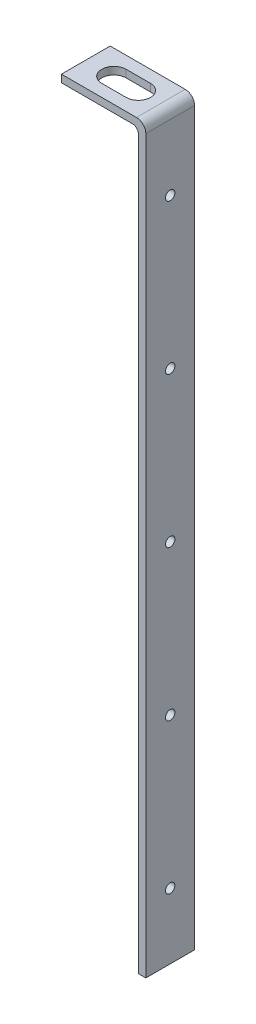
SolidWorks part; units mm, degrees
material "AISI 304"
ref_plane "Front Plane" through (0, 0, 0) normal (0, 0, 1) x (1, 0, 0)
ref_plane "Top Plane" through (0, 0, 0) normal (0, 1, 0) x (1, 0, 0)
ref_plane "Right Plane" through (0, 0, 0) normal (1, 0, 0) x (0, 0, -1)
sketch "Sketch1" plane through (0, 0, 0) normal (0, 0, 1) x (1, 0, 0)
  line L0 (0, 0) -> (0, 395)
  line L1 (0, 395) -> (-45, 395)
  line L6 (-4, 0) -> (-4, 391)
  line L7 (-4, 391) -> (-45, 391)
  line L8 (-45, 395) -> (-45, 391)
  line L9 (-4, 0) -> (0, 0)
  dimension "D1" = 395
  dimension "D2" = 45
  dimension "D3" = 4
extrude "Boss-Extrude1" add sketch "Sketch1" along normal blind 26
sketch "Sketch2" plane through (0, 0, 0) normal (1, 0, 0) x (0, 0, -1)
  line L1 (-26, 0) -> (0, 0) construction
  circle A0 centre (-13, 195) radius 2.5
  circle A1 centre (-13, 115) radius 2.5
  circle A2 centre (-13, 35) radius 2.5
  circle A3 centre (-13, 275) radius 2.5
  circle A4 centre (-13, 355) radius 2.5
  point P10 (-13, 0)
  dimension "D4" = 5
  dimension "D1" = 35
  dimension "D2" = 80
  dimension "D3" = 80
  dimension "D5" = 80
  dimension "D6" = 80
extrude "Cut-Extrude1" cut sketch "Sketch2" against normal through all
sketch "Sketch3" plane through (0, 395, 0) normal (0, 1, 0) x (1, 0, 0)
  line L0 (0, -26) -> (0, 0) construction
  line L1 (-30, -13) -> (-17, -13) construction
  line L2 (-30, -6.5) -> (-17, -6.5)
  line L3 (-30, -19.5) -> (-17, -19.5)
  arc A1 (-30, -6.5) -> (-30, -19.5) centre (-30, -13) ccw
  arc A2 (-17, -19.5) -> (-17, -6.5) centre (-17, -13) ccw
  point P2 (-23.5, -13)
  point P5 (0, -13)
  dimension "D4" = 6.5
  dimension "D1" = 30
  dimension "D3" = 13
extrude "Cut-Extrude2" cut sketch "Sketch3" against normal through all
fillet "Fillet1" radius 3 1 edges at (-4, 391, 13)
fillet "Fillet2" radius 5 1 edges at (0, 395, 13)
